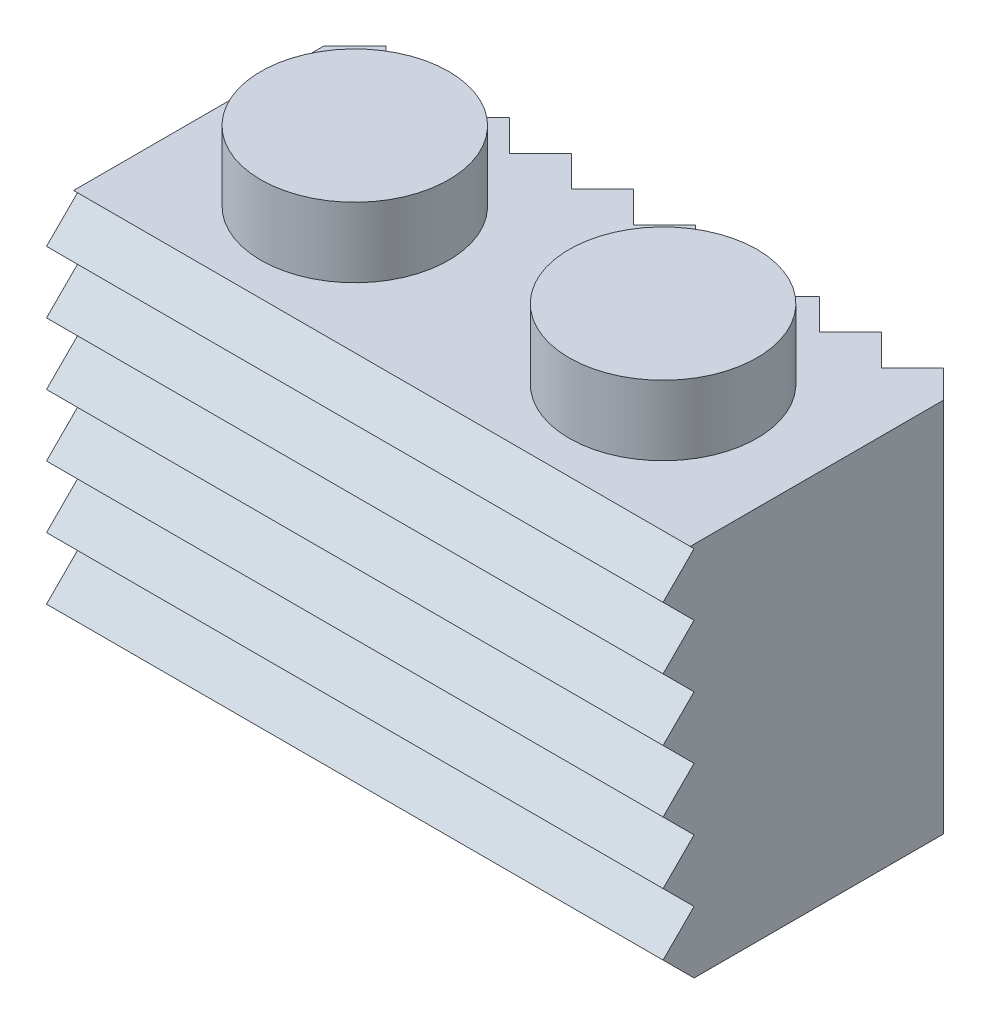
SolidWorks part; units mm, degrees
ref_plane "Front Plane" through (0, 0, 0) normal (0, 0, 1) x (1, 0, 0)
ref_plane "Top Plane" through (0, 0, 0) normal (0, 1, 0) x (1, 0, 0)
ref_plane "Right Plane" through (0, 0, 0) normal (1, 0, 0) x (0, 0, -1)
sketch "Sketch1" plane through (0, 0, 0) normal (0, 1, 0) x (1, 0, 0)
  line L1 (-3.98, 3.98) -> (3.98, 3.98)
  line L2 (-3.98, 3.98) -> (-3.98, -3.98)
  line L3 (-3.98, -3.98) -> (3.98, -3.98)
  line L4 (3.98, 3.98) -> (3.98, -3.98)
  line L5 (-3.98, 3.98) -> (3.98, -3.98) construction
  line L6 (-3.98, -3.98) -> (3.98, 3.98) construction
  point P0 (0, 0)
  dimension "D1" = 7.96
extrude "Extrude1" add sketch "Sketch1" along normal blind 9.7
sketch "Sketch2" plane through (0, 9.7, 0) normal (0, 1, 0) x (1, 0, 0)
  circle A0 centre (0, 0) radius 2.425
  dimension "D1" = 4.85
extrude "Extrude2" add sketch "Sketch2" along normal blind 1.8
pattern_linear "LPattern1" count 2 spacing 7.96 along (1, 0, 0) of "Extrude2", "Extrude1"
shell "Shell1" thickness 1.55
sketch "Sketch3" plane through (0, 8.15, 0) normal (0, -1, 0) x (1, 0, 0)
  line L0 (10.39, -2.43) -> (-2.43, -2.43) construction
  line L1 (-2.43, -2.43) -> (-2.43, 2.43) construction
  line L2 (-2.43, 2.43) -> (10.39, 2.43) construction
  line L3 (10.39, 2.43) -> (10.39, -2.43) construction
  line L4 (10.39, -2.43) -> (-2.43, -2.43)
  line L5 (-2.43, -2.43) -> (-2.43, 2.43)
  line L6 (-2.43, 2.43) -> (10.39, 2.43)
  line L7 (10.39, 2.43) -> (10.39, -2.43)
extrude "Extrude3" cut sketch "Sketch3" against normal blind 0.14
sketch "Sketch4" plane through (0, 8.29, 0) normal (0, -1, 0) x (1, 0, 0)
  line L0 (-2.43, 2.43) -> (10.39, 2.43) construction
  circle A0 centre (3.98, 0) radius 1.5
  point P4 (3.98, 2.43)
  dimension "D1" = 3
extrude "Extrude4" add sketch "Sketch4" along normal up to surface (8.29 mm away) up to face at (3.98, 0, 0)
sketch "Sketch5" plane through (0, 8.29, 0) normal (0, -1, 0) x (1, 0, 0)
  line L0 (10.39, -2.43) -> (-2.43, -2.43) construction
  line L1 (3.48, 2.43) -> (4.48, 2.43)
  line L2 (3.48, 2.43) -> (3.48, -2.43)
  line L3 (3.48, -2.43) -> (4.48, -2.43)
  line L4 (4.48, 2.43) -> (4.48, -2.43)
  line L5 (3.48, 2.43) -> (4.48, -2.43) construction
  line L6 (3.48, -2.43) -> (4.48, 2.43) construction
  point P0 (3.98, 0)
  dimension "D1" = 1
extrude "Extrude5" add sketch "Sketch5" along normal offset from surface (6.29 mm away) 2 up to face at (3.98, 0, 0)
sketch "Sketch7" plane through (11.94, 0, 0) normal (1, 0, 0) x (0, 0, -1)
  line L0 (-3.98, -0.8) -> (-3.18, 0)
  line L1 (-3.98, 9.7) -> (-3.98, 0) construction
  line L2 (-3.18, 0) -> (-3.98, 0.8)
  line L3 (-3.98, 0.8) -> (-3.98, -0.8)
  line L4 (-3.98, 0) -> (3.98, 0) construction
  dimension "D1" = 1.6
extrude "Extrude6" cut sketch "Sketch7" against normal through all
pattern_linear "LPattern2" count 7 spacing 1.6 along (0, 0.7071, -0.7071) of "Extrude6"
sketch "Sketch8" plane through (0, 9.7, 0) normal (0, 1, 0) x (1, 0, 0)
  line L0 (-3.98, 3.18) -> (-3.18, 3.98)
  line L1 (-3.98, 3.98) -> (-3.98, -3.28) construction
  line L2 (11.94, 3.98) -> (-3.98, 3.98) construction
  line L3 (-3.18, 3.98) -> (-4.78, 3.98)
  line L4 (-4.78, 3.98) -> (-3.98, 3.18)
  dimension "D1" = 1.6
  dimension "D2" = 0.8
extrude "Extrude7" cut sketch "Sketch8" against normal through all
pattern_linear "LPattern3" count 11 spacing 1.6 along (0.7071, 0, 0.7071) of "Extrude7"
